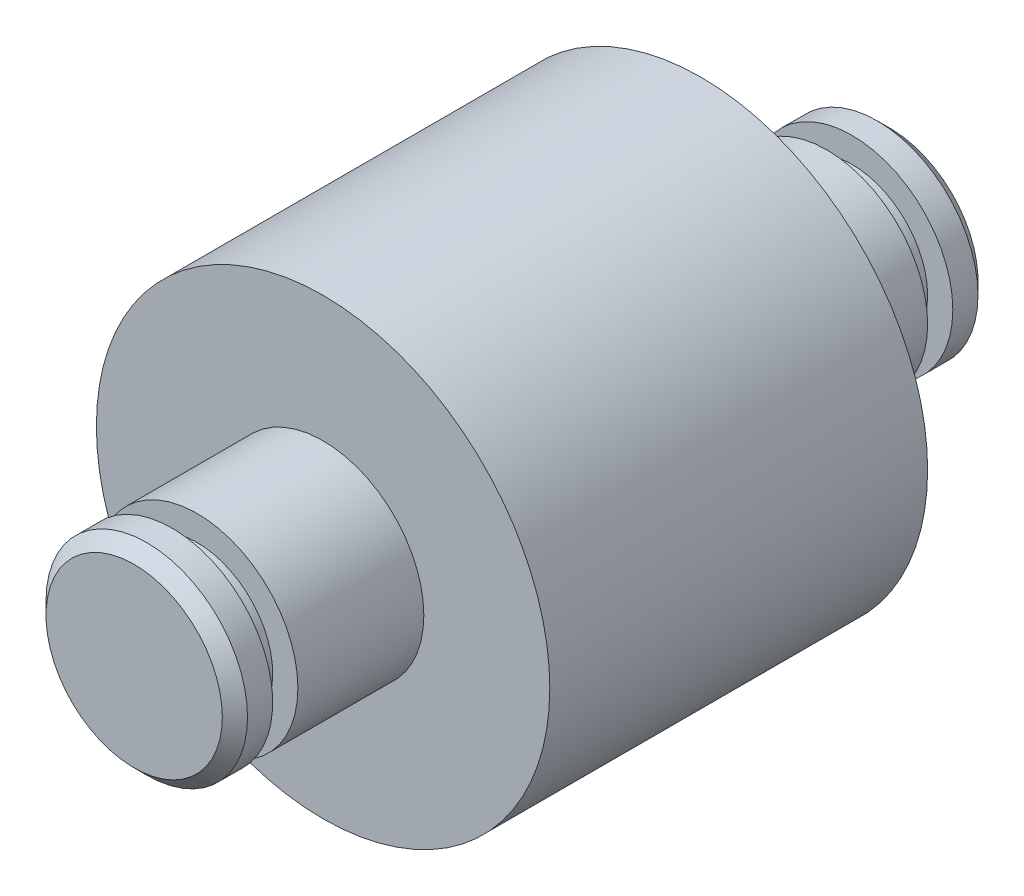
SolidWorks part; units mm, degrees
material "Plain Carbon Steel"
ref_plane "Front Plane" through (0, 0, 0) normal (0, 0, 1) x (1, 0, 0)
ref_plane "Top Plane" through (0, 0, 0) normal (0, 1, 0) x (1, 0, 0)
ref_plane "Right Plane" through (0, 0, 0) normal (1, 0, 0) x (0, 0, -1)
sketch "Sketch1" plane through (0, 0, 0) normal (0, 0, 1) x (1, 0, 0)
  circle A0 centre (0, 0) radius 9
  dimension "D1" = 18
extrude "Boss-Extrude1" add sketch "Sketch1" along normal blind 7.5
sketch "Sketch2" plane through (0, 0, 7.5) normal (0, 0, 1) x (1, 0, 0)
  circle A0 centre (0, 0) radius 4
  dimension "D1" = 8
extrude "Boss-Extrude2" add sketch "Sketch2" along normal blind 7.5
sketch "Sketch3" plane through (0, 0, 0) normal (1, 0, 0) x (0, 0, -1)
  line L0 (-15, 0) -> (0, 0) construction
  line L1 (-15, 4) -> (-15, -4) construction
  line L3 (-13.5, 4.614) -> (-12.5, 4.614)
  line L4 (-13.5, 4.614) -> (-13.5, 3)
  line L5 (-13.5, 3) -> (-12.5, 3)
  line L6 (-12.5, 4.614) -> (-12.5, 3)
  dimension "D1" = 1
  dimension "D2" = 3
  dimension "D3" = 1.5
revolve "Cut-Revolve1" cut sketch "Sketch3" angle 360 about L0
chamfer "Chamfer1" distance 0.5 angle 45 1 edges at (4, 0, 15)
mirror "Mirror1" about plane through (0, 0, 0) normal (0, 0, 1) of "Boss-Extrude1", "Cut-Revolve1", "Boss-Extrude2", "Chamfer1"
